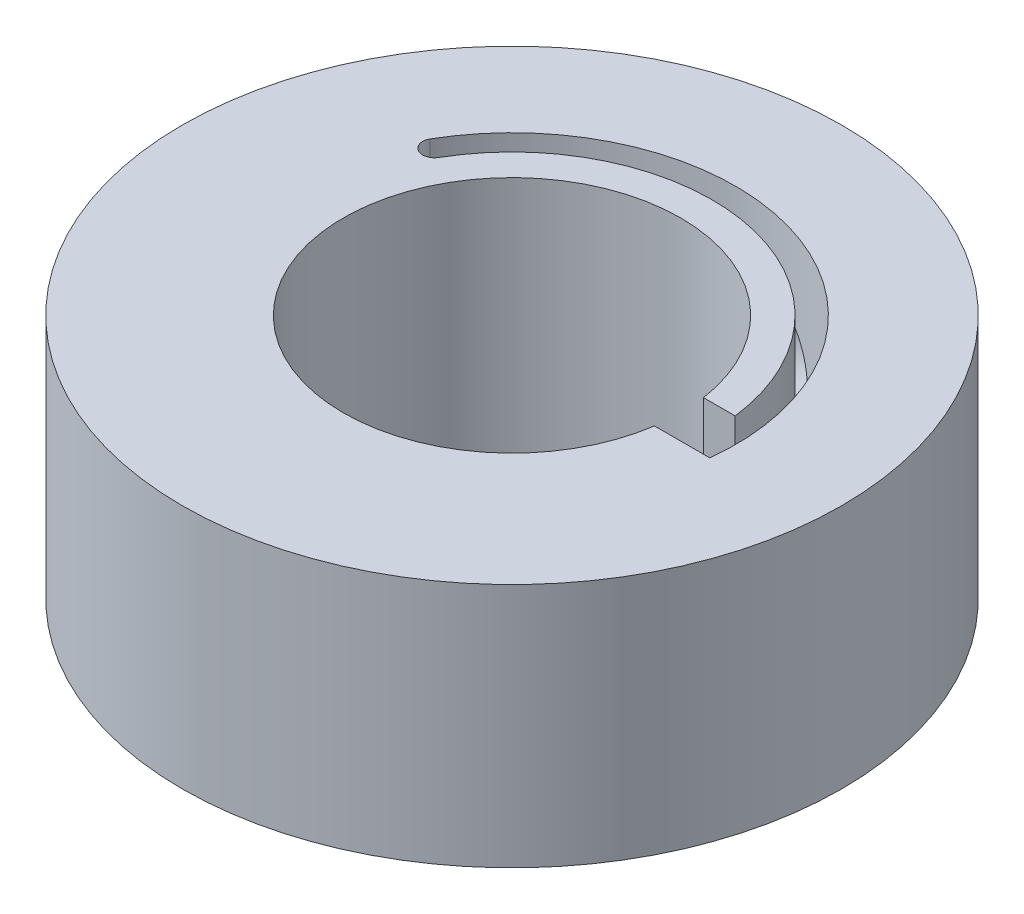
SolidWorks part; units mm, degrees
ref_plane "Front" through (0, 0, 0) normal (0, 0, 1) x (1, 0, 0)
ref_plane "Top" through (0, 0, 0) normal (0, 1, 0) x (1, 0, 0)
ref_plane "Right" through (0, 0, 0) normal (1, 0, 0) x (0, 0, -1)
sketch "Sketch1" plane through (0, 0, 0) normal (0, 1, 0) x (1, 0, 0)
  line L0 (10.806, 1.5875) -> (12.8564, 1.5875)
  line L1 (10.806, -1.5875) -> (14.3907, -1.5875)
  line L2 (10.806, 1.5875) -> (0, 0) construction
  line L3 (0, 0) -> (10.806, -1.5875) construction
  line L4 (-11.8784, 6.858) -> (0, 0) construction
  line L5 (0, 0) -> (11.1431, 0) construction
  circle A0 centre (0, 0) radius 21.336
  arc A1 (10.806, 1.5875) -> (10.806, -1.5875) centre (0, 0) ccw
  arc A2 (-11.2185, 6.477) -> (12.8564, 1.5875) centre (0, 0) cw
  arc A3 (14.3907, -1.5875) -> (-12.5383, 7.239) centre (0, 0) ccw
  arc A4 (-12.5383, 7.239) -> (-11.2185, 6.477) centre (-11.8784, 6.858) ccw
  dimension "D1" = 42.672
  dimension "D2" = 21.844
  dimension "D3" = 2.032
  dimension "D5" = 1.524
  dimension "D7" = 6.858
  dimension "D4" = 3.175
  dimension "D6" = 150
extrude "Boss-Extrude1" add sketch "Sketch1" along normal mid plane 15.875
sketch "Sketch2" plane through (0, 0, 0) normal (0, 1, 0) x (1, 0, 0)
  line L0 (-0.3, 14.4749) -> (2.8114, 13.843)
  line L1 (2.8114, 13.843) -> (4.2466, 20.9091)
  line L2 (4.2466, 20.9091) -> (1.1351, 21.5411)
  line L3 (1.1351, 21.5411) -> (-0.3, 14.4749)
  line L4 (2.8114, 13.843) -> (1.6634, 8.1903) construction
  line L5 (-11.2185, 6.477) -> (2.8114, 13.843) construction
  line L6 (12.8564, 1.5875) -> (2.8114, 13.843) construction
  arc A0 (14.3907, -1.5875) -> (-12.5383, 7.239) centre (0, 0) ccw construction
  circle A1 centre (0, 0) radius 21.336 construction
  arc A3 (12.8564, 1.5875) -> (-11.2185, 6.477) centre (0, 0) ccw construction
  point P19 (12.8564, 1.5875)
  dimension "D1" = 6.35
revolve "Cut-Revolve1" cut sketch "Sketch2" angle 360 about L4
